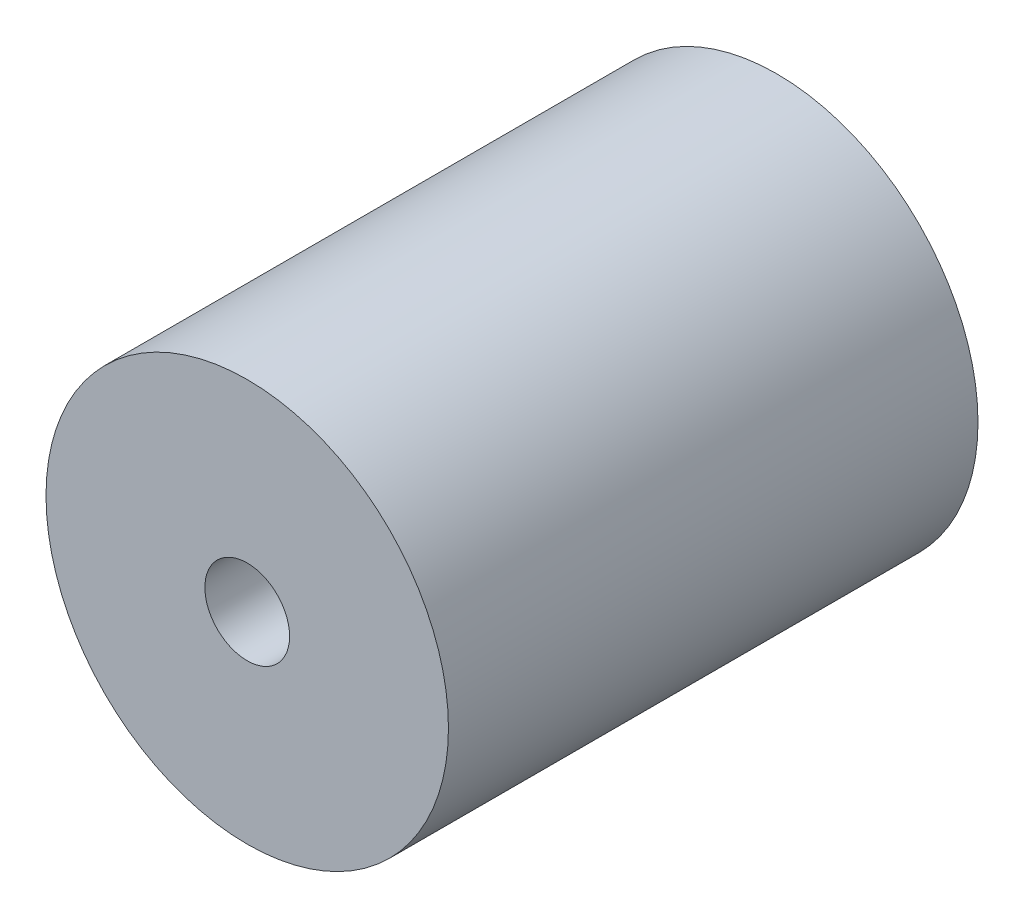
SolidWorks part; units mm, degrees
ref_plane "Front" through (0, 0, 0) normal (0, 0, 1) x (1, 0, 0)
ref_plane "Top" through (0, 0, 0) normal (0, 1, 0) x (1, 0, 0)
ref_plane "Right" through (0, 0, 0) normal (1, 0, 0) x (0, 0, -1)
sketch "Sketch1" plane through (0, 0, 0) normal (0, 0, 1) x (1, 0, 0)
  circle A0 centre (0, 0) radius 9.5
  dimension "D1" = 19
extrude "Boss-Extrude1" add sketch "Sketch1" along normal blind 25
sketch "Sketch2" plane through (0, 0, 25) normal (0, 0, 1) x (1, 0, 0)
  circle A0 centre (0, 0) radius 2
  dimension "D1" = 4
extrude "Cut-Extrude1" cut sketch "Sketch2" against normal through all
sketch "Sketch3" plane through (0, 0, 0) normal (0, 0, -1) x (-1, 0, 0)
  circle A0 centre (0, 0) radius 5
  dimension "D1" = 10
extrude "Cut-Extrude2" cut sketch "Sketch3" against normal blind 12.5
